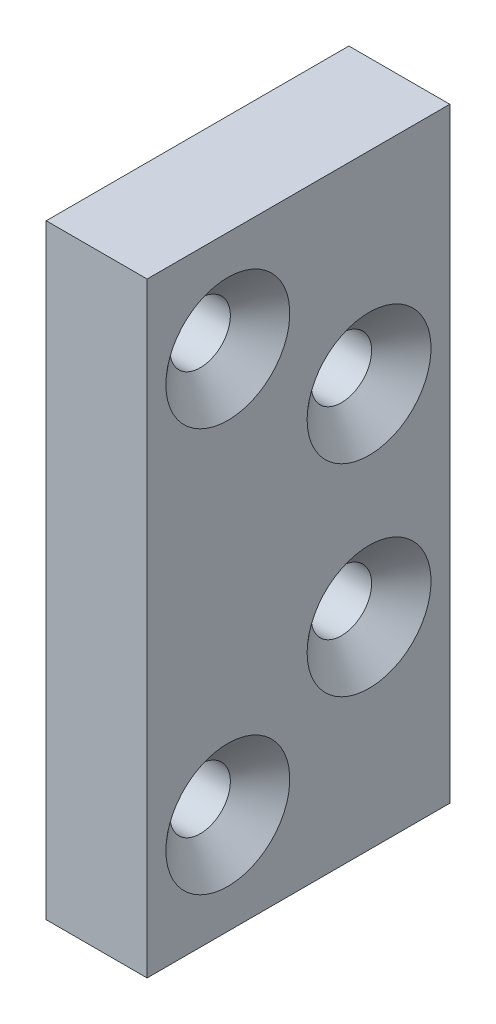
SolidWorks part; units mm, degrees
material "AISI Type A2 Tool Steel"
ref_plane "Front Plane" through (0, 0, 0) normal (0, 0, 1) x (1, 0, 0)
ref_plane "Top Plane" through (0, 0, 0) normal (0, 1, 0) x (1, 0, 0)
ref_plane "Right Plane" through (0, 0, 0) normal (1, 0, 0) x (0, 0, -1)
sketch "Sketch1" plane through (0, 0, 0) normal (1, 0, 0) x (0, 0, -1)
  line L0 (-1000, 0) -> (49000, 0) construction
  line L1 (-9.525, -19.05) -> (9.525, -19.05)
  line L2 (-9.525, -19.05) -> (-9.525, 19.05)
  line L3 (-9.525, 19.05) -> (9.525, 19.05)
  line L4 (9.525, -19.05) -> (9.525, 19.05)
  line L5 (-9.525, -19.05) -> (9.525, 19.05) construction
  line L6 (-9.525, 19.05) -> (9.525, -19.05) construction
  circle A0 centre (-4.445, 12.7) radius 1.8987
  circle A1 centre (4.445, 6.35) radius 1.8986
  circle A2 centre (-4.445, -12.7) radius 1.8987
  circle A3 centre (4.445, -6.35) radius 1.8986
  point P0 (0, 0)
  dimension "D3" = 3.7973
  dimension "D1" = 19.05
  dimension "D2" = 38.1
  dimension "D4" = 12.7
  dimension "D5" = 5.08
  dimension "D6" = 5.08
  dimension "D7" = 6.35
extrude "Boss-Extrude1" add sketch "Sketch1" along normal blind 6.35
chamfer "Chamfer1" distance 2.0002 angle 41 4 edges at (6.35, -6.35, -2.5463) (6.35, -12.7, 6.3437) (6.35, 6.35, -6.3436) (6.35, 12.7, 2.5464)
